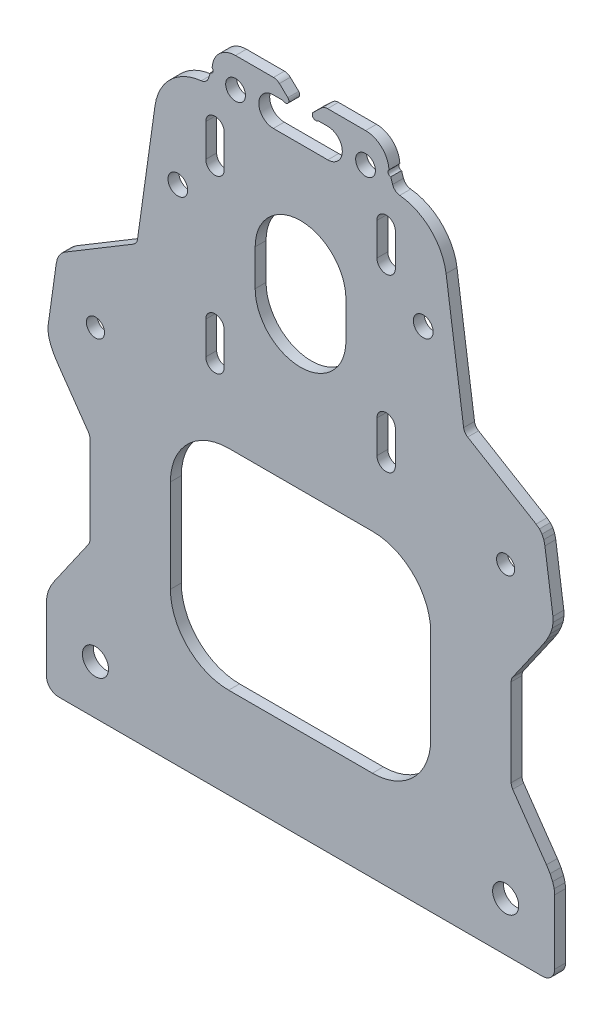
SolidWorks part; units mm, degrees
ref_plane "Front" through (0, 0, 0) normal (0, 0, 1) x (1, 0, 0)
ref_plane "Top" through (0, 0, 0) normal (0, 1, 0) x (1, 0, 0)
ref_plane "Right" through (0, 0, 0) normal (1, 0, 0) x (0, 0, -1)
sketch "Model" plane through (0, 0, 0) normal (0, 0, 1) x (1, 0, 0)
  line L0 (-66.6404, 0) -> (66.6403, 0)
  line L1 (-69.9997, 21.1105) -> (-69.9997, 3.3593)
  line L2 (-69.5175, 87.3083) -> (-67.3079, 103.0302)
  line L3 (-67.3079, 103.0302) -> (-66.9899, 104.3736)
  line L4 (-66.9899, 104.3736) -> (-66.4641, 105.4734)
  line L5 (-66.4641, 105.4734) -> (-65.7645, 106.3363)
  line L6 (-65.7645, 106.3363) -> (-64.8747, 107.0176)
  line L7 (-69.9997, 21.1105) -> (-69.8655, 22.4981)
  line L8 (-69.8655, 22.4981) -> (-69.4453, 23.9884)
  line L9 (-69.4453, 23.9884) -> (-68.7321, 25.549)
  line L10 (-68.7321, 25.549) -> (-67.7328, 27.1616)
  line L11 (3.5003, 174.5536) -> (5.8203, 176.7548)
  line L12 (-19.8029, 25.0481) -> (19.8036, 25.0481)
  line L13 (-58.4275, 67.2803) -> (-66.7857, 79.2679)
  line L14 (-66.7857, 79.2679) -> (-67.9147, 81.0492)
  line L15 (-67.9147, 81.0492) -> (-68.7631, 82.7614)
  line L16 (-68.7631, 82.7614) -> (-69.3163, 84.3925)
  line L17 (-69.3163, 84.3925) -> (-69.5643, 85.9155)
  line L18 (-69.5643, 85.9155) -> (-69.5175, 87.3083)
  line L19 (-58.0053, 41.8651) -> (-58.0053, 65.9363)
  line L20 (-44.9176, 120.0252) -> (-40.0933, 154.3521)
  line L21 (-25.3495, 168.249) -> (-24.8281, 169.8174)
  line L22 (-64.8747, 107.0176) -> (-46.0344, 118.338)
  line L23 (-35.8497, 66.7013) -> (-35.8497, 41.0949)
  line L24 (-26.1097, 157.54) -> (-26.1097, 148.54)
  line L25 (-26.1097, 110.4) -> (-26.1097, 101.4)
  line L26 (-21.0297, 101.4) -> (-21.0297, 110.4)
  line L27 (-21.0297, 148.54) -> (-21.0297, 157.54)
  line L28 (-67.7328, 27.1616) -> (-58.4269, 40.5219)
  line L29 (-12.4997, 134.47) -> (-12.4997, 124.47)
  line L30 (19.8036, 82.7481) -> (-19.8029, 82.7481)
  line L31 (12.5003, 124.47) -> (12.5003, 134.47)
  line L32 (21.0304, 157.54) -> (21.0304, 148.54)
  line L33 (21.0304, 110.4) -> (21.0304, 101.4)
  line L34 (58.4317, 40.5252) -> (67.7348, 27.1616)
  line L35 (26.1103, 101.4) -> (26.1103, 110.4)
  line L36 (26.1103, 148.54) -> (26.1103, 157.54)
  line L37 (35.8504, 41.0949) -> (35.8504, 66.7013)
  line L38 (46.0351, 118.338) -> (64.8754, 107.0176)
  line L39 (24.8288, 169.8174) -> (25.3502, 168.249)
  line L40 (40.094, 154.3521) -> (44.9183, 120.0252)
  line L41 (58.0103, 65.9397) -> (58.0103, 41.8678)
  line L42 (66.7838, 79.2679) -> (58.4323, 67.2832)
  line L43 (64.8754, 107.0176) -> (65.7822, 106.3199)
  line L44 (65.7822, 106.3199) -> (66.4875, 105.4379)
  line L45 (66.4875, 105.4379) -> (66.9996, 104.3501)
  line L46 (66.9996, 104.3501) -> (67.3095, 103.0302)
  line L47 (-5.8196, 176.7548) -> (-3.4996, 174.5536)
  line L48 (70.0003, 21.1105) -> (69.8663, 22.4981)
  line L49 (69.8663, 22.4981) -> (69.4463, 23.9884)
  line L50 (69.4463, 23.9884) -> (68.7335, 25.5489)
  line L51 (68.7335, 25.5489) -> (67.7348, 27.1616)
  line L52 (67.3095, 103.0302) -> (69.5191, 87.3083)
  line L53 (69.5191, 87.3083) -> (69.5654, 85.916)
  line L54 (69.5654, 85.916) -> (69.3167, 84.3947)
  line L55 (69.3167, 84.3947) -> (68.7632, 82.7647)
  line L56 (68.7632, 82.7647) -> (67.9141, 81.0517)
  line L57 (67.9141, 81.0517) -> (66.7838, 79.2679)
  line L58 (70.0003, 3.36) -> (70.0003, 21.1105)
  line L59 (-7.4996, 165.2073) -> (7.5003, 165.2073)
  line L60 (7.5003, 173.2073) -> (4.8467, 173.2073)
  line L61 (-4.846, 173.2073) -> (-7.4996, 173.2073)
  line L62 (17.9111, 177.4) -> (7.4378, 177.4)
  line L63 (-7.4371, 177.4) -> (-17.9104, 177.4)
  arc A0 (-19.8029, 82.7481) -> (-35.8497, 66.7013) centre (-19.8028, 66.7013) ccw
  arc A1 (-35.8497, 41.0949) -> (-19.8029, 25.0481) centre (-19.8029, 41.0949) ccw
  circle A2 centre (-56.4996, 13.52) radius 3.6
  arc A3 (-69.9997, 3.3593) -> (-66.6404, 0) centre (-66.6403, 3.3593) ccw
  arc A4 (-58.0053, 65.9363) -> (-58.4275, 67.2803) centre (-60.3552, 65.9363) ccw
  arc A5 (-58.4269, 40.5219) -> (-58.0053, 41.8651) centre (-60.3553, 41.8651) ccw
  arc A6 (-27.3372, 166.653) -> (-40.0933, 154.3521) centre (-25.8547, 152.351) ccw
  arc A7 (-17.9104, 177.4) -> (-24.3548, 171.2408) centre (-17.9104, 170.949) ccw
  arc A8 (-7.4996, 173.2073) -> (-7.4996, 165.2073) centre (-7.4996, 169.2073) ccw
  circle A9 centre (-17.8997, 169.2073) radius 2.725
  circle A10 centre (-33.7996, 138.65) radius 2.725
  arc A11 (-21.0297, 157.54) -> (-26.1097, 157.54) centre (-23.5696, 157.54) ccw
  arc A12 (-26.1097, 148.54) -> (-21.0297, 148.54) centre (-23.5696, 148.54) ccw
  arc A13 (-21.0297, 110.4) -> (-26.1097, 110.4) centre (-23.5696, 110.4) ccw
  arc A14 (-26.1097, 101.4) -> (-21.0297, 101.4) centre (-23.5696, 101.4) ccw
  circle A15 centre (-56.4996, 93.22) radius 2.5
  arc A16 (-46.0344, 118.338) -> (-44.9176, 120.0252) centre (-47.2448, 120.3523) ccw
  arc A17 (-27.3372, 166.653) -> (-25.3495, 168.249) centre (-27.5795, 168.9904) ccw
  arc A18 (-5.8196, 176.7548) -> (-7.4371, 177.4) centre (-7.4371, 175.05) ccw
  arc A19 (-4.846, 173.2073) -> (-3.4996, 174.5536) centre (-4.1728, 173.8805) ccw
  arc A20 (-24.8281, 169.8174) -> (-24.3548, 171.2408) centre (-24.888, 170.6277) ccw
  arc A21 (19.8036, 25.0481) -> (35.8504, 41.0949) centre (19.8036, 41.0949) ccw
  arc A22 (35.8504, 66.7013) -> (19.8036, 82.7481) centre (19.8036, 66.7013) ccw
  circle A23 centre (56.5004, 13.52) radius 3.6
  arc A24 (66.6403, 0) -> (70.0003, 3.36) centre (66.6403, 3.36) ccw
  arc A25 (58.4323, 67.2832) -> (58.0103, 65.9397) centre (60.3603, 65.9397) ccw
  arc A26 (58.0103, 41.8678) -> (58.4317, 40.5252) centre (60.3603, 41.8678) ccw
  arc A27 (40.094, 154.3521) -> (27.3379, 166.653) centre (25.8554, 152.351) ccw
  arc A28 (12.5003, 134.47) -> (-12.4997, 134.47) centre (0.0004, 134.47) ccw
  arc A29 (-12.4997, 124.47) -> (12.5003, 124.47) centre (0.0004, 124.47) ccw
  arc A30 (24.3555, 171.2408) -> (17.9111, 177.4) centre (17.9111, 170.949) ccw
  arc A31 (7.5003, 165.2073) -> (7.5003, 173.2073) centre (7.5003, 169.2073) ccw
  circle A32 centre (17.9004, 169.2073) radius 2.725
  circle A33 centre (33.8004, 138.65) radius 2.725
  arc A34 (26.1103, 157.54) -> (21.0304, 157.54) centre (23.5703, 157.54) ccw
  arc A35 (21.0304, 148.54) -> (26.1103, 148.54) centre (23.5703, 148.54) ccw
  arc A36 (26.1103, 110.4) -> (21.0304, 110.4) centre (23.5703, 110.4) ccw
  arc A37 (21.0304, 101.4) -> (26.1103, 101.4) centre (23.5703, 101.4) ccw
  circle A38 centre (56.5004, 93.22) radius 2.5
  arc A39 (44.9183, 120.0252) -> (46.0351, 118.338) centre (47.2455, 120.3523) ccw
  arc A40 (25.3502, 168.249) -> (27.3379, 166.653) centre (27.5802, 168.9904) ccw
  arc A41 (7.4378, 177.4) -> (5.8203, 176.7548) centre (7.4378, 175.05) ccw
  arc A42 (3.5003, 174.5536) -> (4.8467, 173.2073) centre (4.1735, 173.8805) ccw
  arc A43 (24.3555, 171.2408) -> (24.8288, 169.8174) centre (24.8887, 170.6277) ccw
extrude "Boss-Extrude1" add sketch "Model" along normal blind 3
